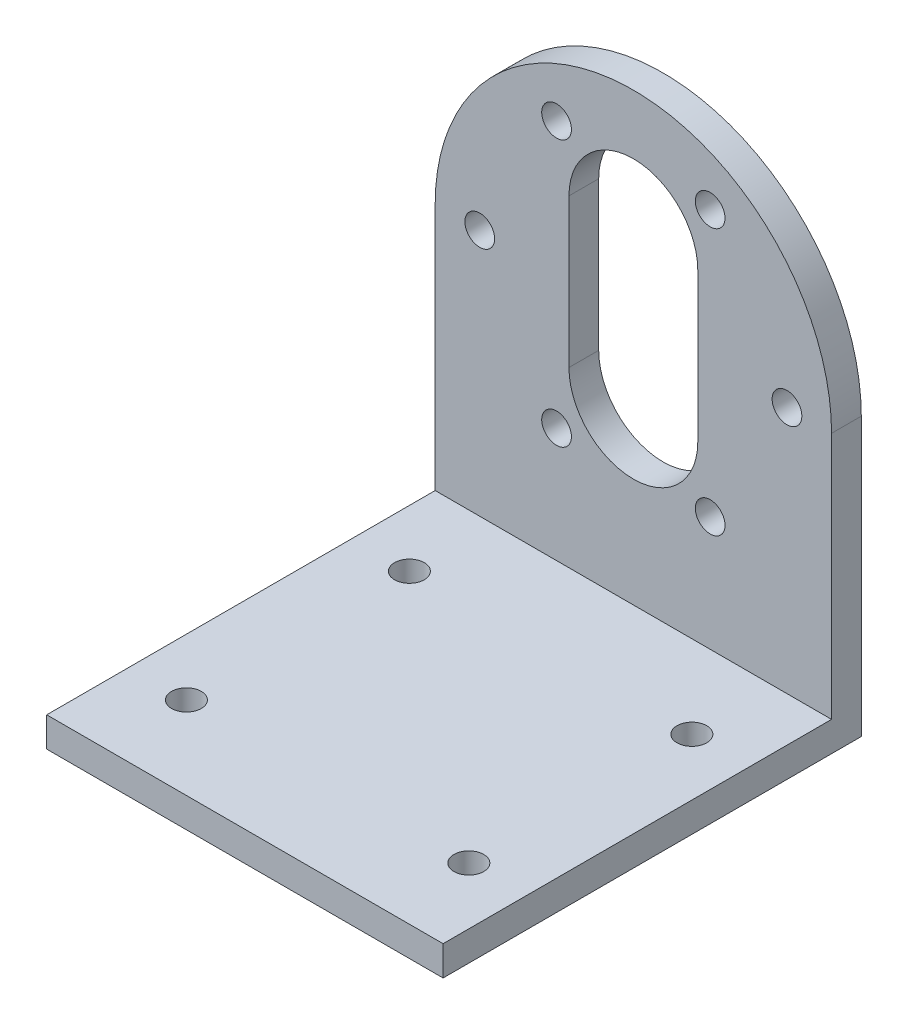
SolidWorks part; units mm, degrees
material "1023 Chapa de aço carbono (SS)"
ref_plane "Plano frontal" through (0, 0, 0) normal (0, 0, 1) x (1, 0, 0)
ref_plane "Plano superior" through (0, 0, 0) normal (0, 1, 0) x (1, 0, 0)
ref_plane "Plano direito" through (0, 0, 0) normal (1, 0, 0) x (0, 0, -1)
sketch "Esboço1" plane through (0, 0, 0) normal (0, 0, 1) x (1, 0, 0)
  line L0 (-20, 0) -> (-20, -28)
  line L1 (-20, -28) -> (20, -28)
  line L2 (20, -28) -> (20, 0)
  line L3 (0, 7.5) -> (0, -7.5) construction
  line L4 (6.5, 7.5) -> (6.5, -7.5)
  line L5 (-6.5, 7.5) -> (-6.5, -7.5)
  arc A0 (20, 0) -> (-20, 0) centre (0, 0) ccw
  arc A1 (6.5, 7.5) -> (-6.5, 7.5) centre (0, 7.5) ccw
  arc A2 (-6.5, -7.5) -> (6.5, -7.5) centre (0, -7.5) ccw
  circle A3 centre (-15.5, 0) radius 1.5
  circle A4 centre (-7.75, 13.4234) radius 1.5
  circle A5 centre (7.75, 13.4234) radius 1.5
  circle A6 centre (15.5, 0) radius 1.5
  circle A7 centre (7.75, -13.4234) radius 1.5
  circle A8 centre (-7.75, -13.4234) radius 1.5
  point P1 (0, 20)
  point P2 (0, 0)
  point P13 (0, 14)
  point P15 (0, -14)
  point P16 (-6.5, 0)
  point P31 (0, 0)
  dimension "D3" = 6.5
  dimension "D5" = 20
  dimension "D6" = 3
  dimension "D1" = 48
  dimension "D2" = 28
  dimension "D4" = 15.5
  dimension "D7" = 6
extrude "Ressalto-extrusão1" add sketch "Esboço1" along normal blind 3
sketch "Esboço2" plane through (0, -28, 0) normal (0, -1, 0) x (1, 0, 0)
  line L0 (0, 3) -> (0, 42.2) construction
  line L1 (20, 0) -> (-20, 0)
  line L2 (20, 0) -> (20, 42.2)
  line L3 (20, 42.2) -> (-20, 42.2)
  line L4 (-20, 0) -> (-20, 42.2)
  line L5 (20, 3) -> (-20, 3) construction
  line L6 (-20, 22.6) -> (20, 22.6) construction
  line L7 (-14.25, 11.35) -> (-14.25, 33.85) construction
  circle A0 centre (-14.25, 11.35) radius 1.5
  circle A1 centre (14.25, 11.35) radius 1.5
  circle A2 centre (14.25, 33.85) radius 1.5
  circle A3 centre (-14.25, 33.85) radius 1.5
  point P14 (0, 22.6)
  dimension "D2" = 3
  dimension "D1" = 42.2
  dimension "D3" = 14.25
  dimension "D4" = 11.25
  dimension "D7" = 22.5
  dimension "D5" = 2
  dimension "D6" = 2
extrude "Ressalto-extrusão2" add sketch "Esboço2" against normal blind 3
